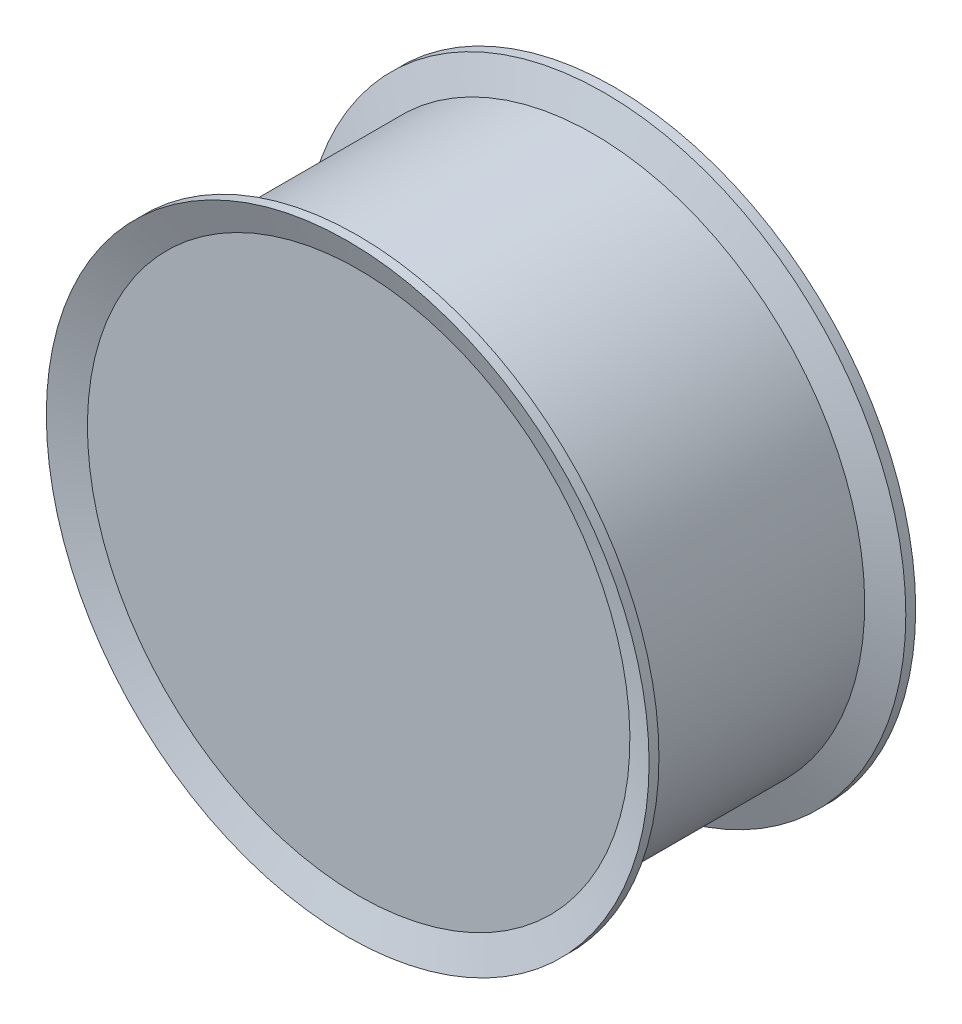
SolidWorks part; units mm, degrees
ref_plane "Front Plane" through (0, 0, 0) normal (0, 0, 1) x (1, 0, 0)
ref_plane "Top Plane" through (0, 0, 0) normal (0, 1, 0) x (1, 0, 0)
ref_plane "Right Plane" through (0, 0, 0) normal (1, 0, 0) x (0, 0, -1)
sketch "Sketch1" plane through (0, 0, 0) normal (1, 0, 0) x (0, 0, -1)
  line L0 (-14.94, 0) -> (14.94, 0) construction
  line L1 (-52.7684, 117) -> (-57.5, 130)
  line L2 (-52.7684, 117) -> (-52.7684, 0)
  line L3 (-52.7684, 0) -> (52.7684, 0)
  line L4 (52.7684, 0) -> (52.7684, 117)
  line L5 (52.7684, 117) -> (57.5, 130)
  line L6 (-57.5, 130) -> (57.5, 130) construction
  line L7 (-53.2433, 130) -> (-48.5117, 117)
  line L8 (-48.5117, 117) -> (48.5117, 117)
  line L9 (48.5117, 117) -> (53.2433, 130)
  line L10 (-57.5, 130) -> (-53.2433, 130)
  line L11 (53.2433, 130) -> (57.5, 130)
  point P5 (0, 0)
  point P11 (0, 117)
  point P13 (0, 130)
  dimension "D1" = 130
  dimension "D2" = 117
  dimension "D3" = 4
  dimension "D4" = 115
  dimension "D5" = 160
revolve "Revolve1" add sketch "Sketch1" angle 360 about L3
